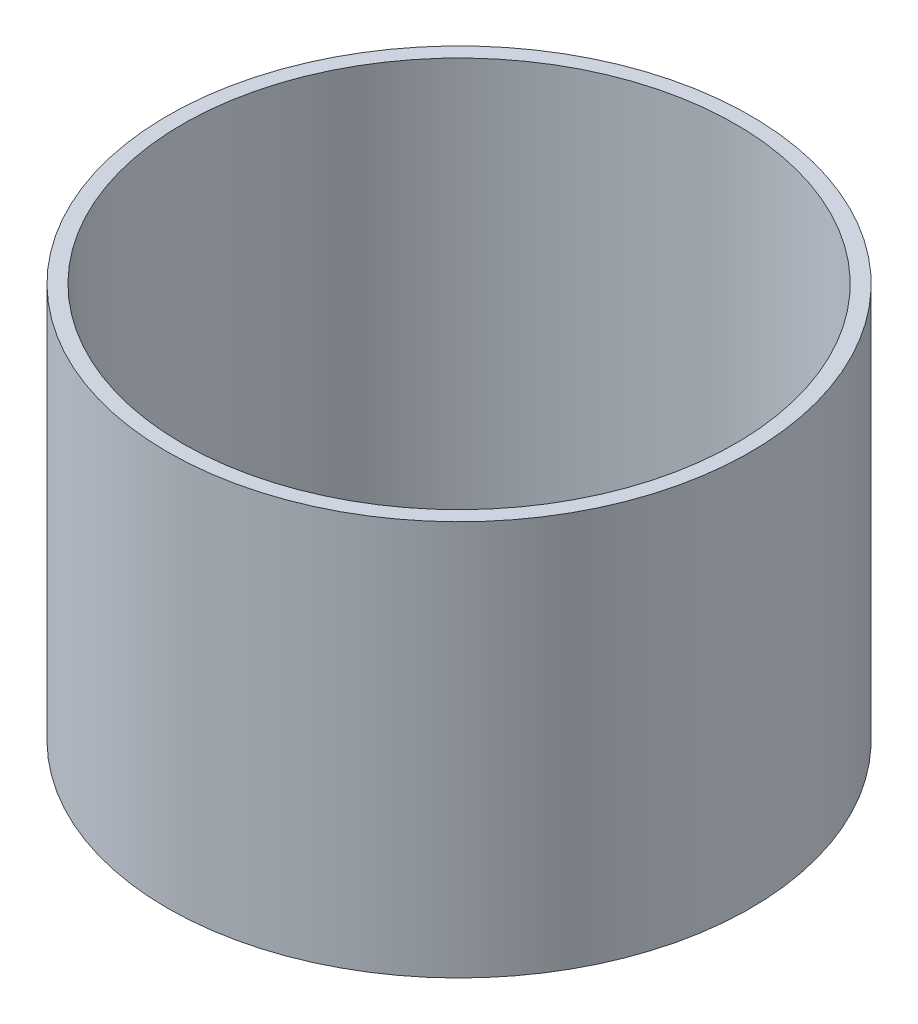
SolidWorks part; units mm, degrees
ref_plane "Front Plane" through (0, 0, 0) normal (0, 0, 1) x (1, 0, 0)
ref_plane "Top Plane" through (0, 0, 0) normal (0, 1, 0) x (1, 0, 0)
ref_plane "Right Plane" through (0, 0, 0) normal (1, 0, 0) x (0, 0, -1)
sketch "Sketch1" plane through (0, 0, 0) normal (0, 1, 0) x (1, 0, 0)
  circle A0 centre (0, 0) radius 93.6625
  circle A1 centre (0, 0) radius 88.9
  dimension "D1" = 187.325
  dimension "D2" = 177.8
extrude "Boss-Extrude1" add sketch "Sketch1" along normal mid plane 127
